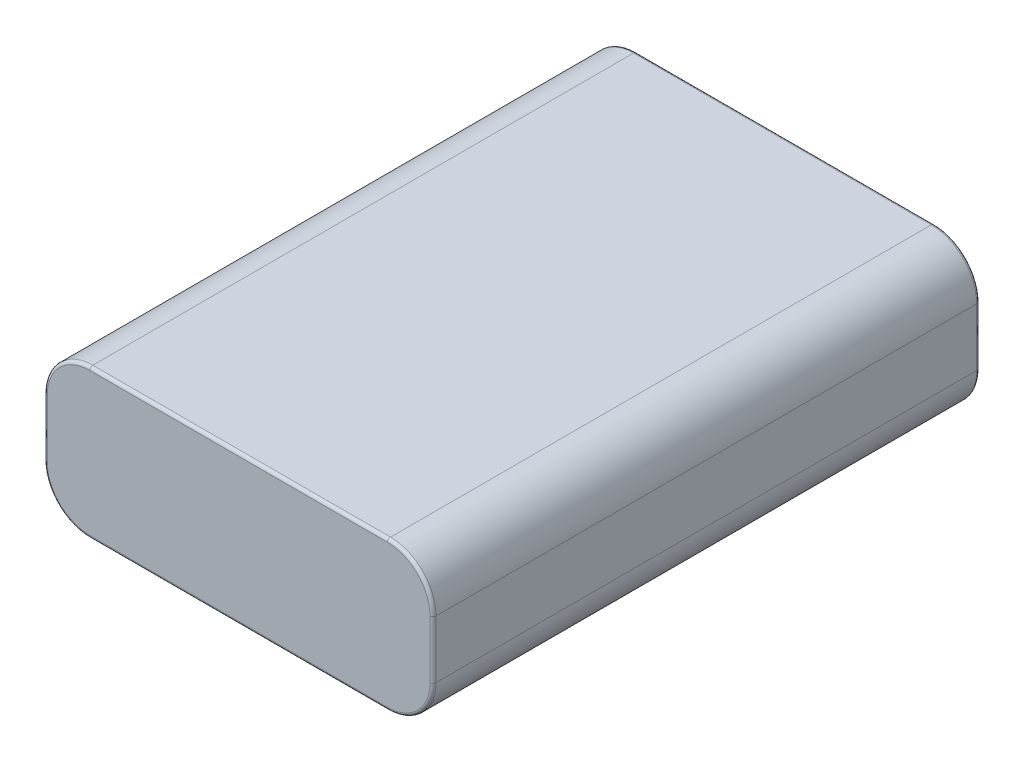
SolidWorks part; units mm, degrees
ref_plane "Alzado" through (0, 0, 0) normal (0, 0, 1) x (1, 0, 0)
ref_plane "Planta" through (0, 0, 0) normal (0, 1, 0) x (1, 0, 0)
ref_plane "Vista lateral" through (0, 0, 0) normal (1, 0, 0) x (0, 0, -1)
sketch "Croquis1" plane through (0, 0, 0) normal (0, 1, 0) x (1, 0, 0)
  line L1 (-32, -45) -> (32, -45)
  line L2 (-32, -45) -> (-32, 45)
  line L3 (-32, 45) -> (32, 45)
  line L4 (32, -45) -> (32, 45)
  line L5 (-32, -45) -> (32, 45) construction
  line L6 (-32, 45) -> (32, -45) construction
  point P0 (0, 0)
  dimension "D1" = 90
  dimension "D2" = 64
extrude "Saliente-Extruir1" add sketch "Croquis1" along normal blind 24.5
fillet "Redondeo1" radius 7.5 4 edges at (-32, 0, 0) (-32, 24.5, 0) (32, 0, 0) (32, 24.5, 0)
fillet "Redondeo2" radius 0.5 16 edges at (29.8033, 2.1967, -45) (32, 12.25, -45) (29.8033, 22.3033, -45) (0, 24.5, -45) (-29.8033, 22.3033, -45) (-32, 12.25, -45) (-29.8033, 2.1967, -45) (0, 0, -45) (-29.8033, 22.3033, 45) (0, 24.5, 45) (29.8033, 22.3033, 45) (32, 12.25, 45) (29.8033, 2.1967, 45) (0, 0, 45) (-29.8033, 2.1967, 45) (-32, 12.25, 45)
